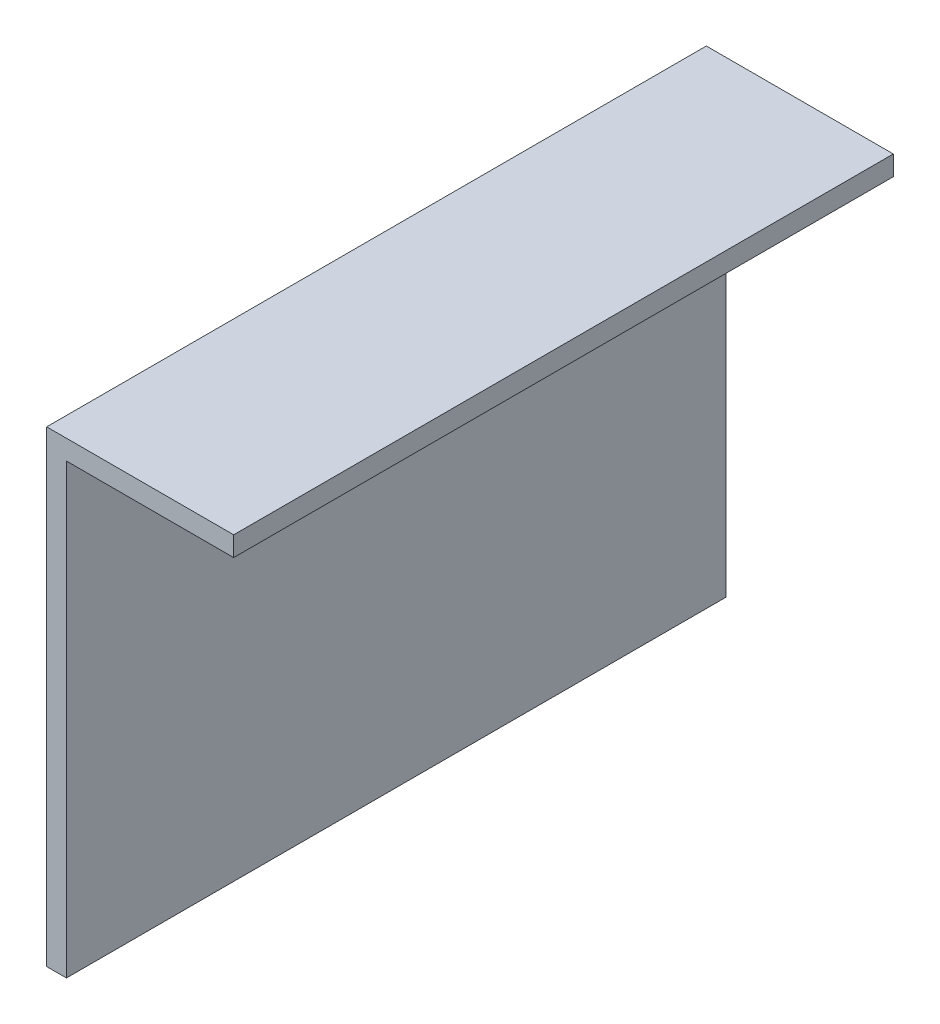
SolidWorks part; units mm, degrees
ref_plane "Alzado" through (0, 0, 0) normal (0, 0, 1) x (1, 0, 0)
ref_plane "Planta" through (0, 0, 0) normal (0, 1, 0) x (1, 0, 0)
ref_plane "Vista lateral" through (0, 0, 0) normal (1, 0, 0) x (0, 0, -1)
sketch "Croquis1" plane through (0, 0, 0) normal (0, 0, 1) x (1, 0, 0)
  line L0 (0, 0) -> (0, 45)
  line L1 (0, 45) -> (18, 45)
  line L2 (1.9, 0) -> (1.9, 43.1)
  line L3 (1.9, 43.1) -> (18, 43.1)
  line L4 (18, 43.1) -> (18, 45)
  line L5 (1.9, 0) -> (0, 0)
  dimension "D1" = 45
  dimension "D2" = 18
  dimension "D3" = 1.9
extrude "Saliente-Extruir1" add sketch "Croquis1" along normal blind 63.5
